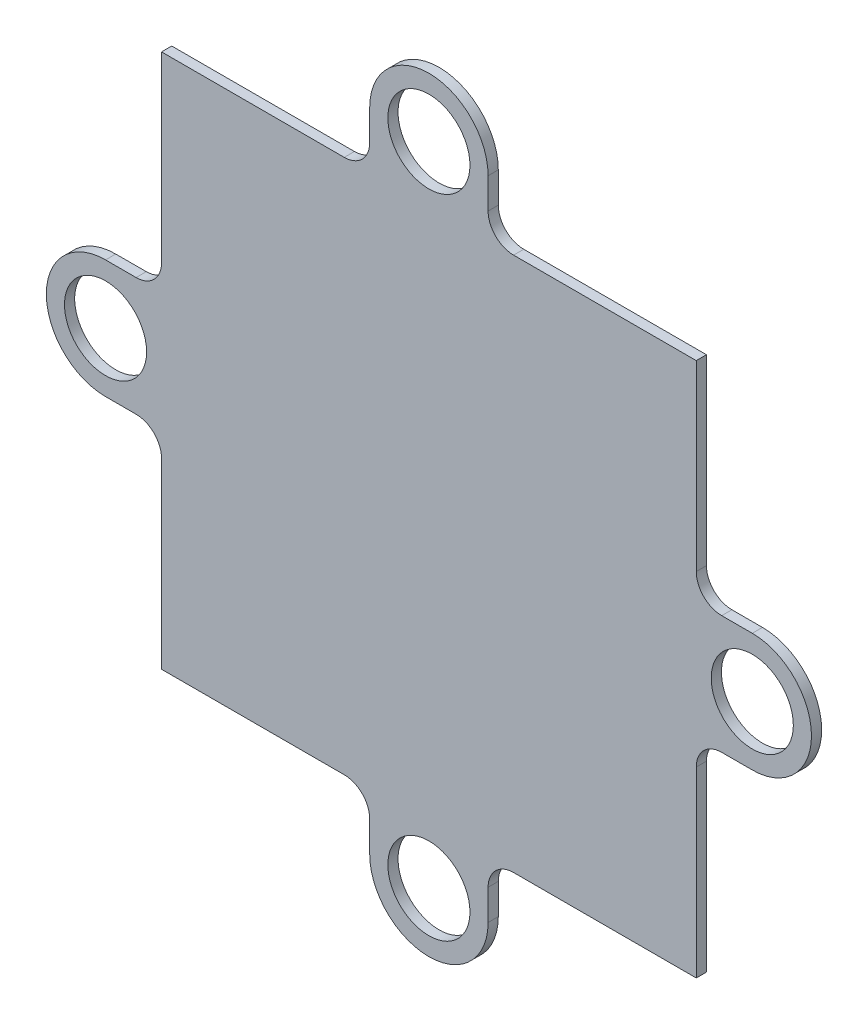
SolidWorks part; units mm, degrees
ref_plane "Front Plane" through (0, 0, 0) normal (0, 0, 1) x (1, 0, 0)
ref_plane "Top Plane" through (0, 0, 0) normal (0, 1, 0) x (1, 0, 0)
ref_plane "Right Plane" through (0, 0, 0) normal (1, 0, 0) x (0, 0, -1)
sketch "Sketch1" plane through (0, 0, 0) normal (0, 0, 1) x (1, 0, 0)
  line L0 (-4.65, 25.4) -> (-4.65, 23)
  line L1 (-21, -21) -> (-6.65, -21)
  line L2 (-21, -21) -> (-21, -6.65)
  line L3 (-21, 21) -> (-6.65, 21)
  line L4 (21, -21) -> (21, -6.65)
  line L5 (-21, -21) -> (21, 21) construction
  line L6 (-21, 21) -> (21, -21) construction
  line L7 (-6.65, 21) -> (-8.7591, 21)
  line L8 (4.65, 25.4) -> (4.65, 23)
  line L9 (6.65, 21) -> (7.1335, 21)
  line L10 (25.4, 4.65) -> (23, 4.65)
  line L11 (21, 6.65) -> (21, 8.7591)
  line L12 (25.4, -4.65) -> (23, -4.65)
  line L13 (21, -6.65) -> (21, -7.1335)
  line L14 (4.65, -25.4) -> (4.65, -23)
  line L15 (6.65, -21) -> (8.7591, -21)
  line L16 (-4.65, -25.4) -> (-4.65, -23)
  line L17 (-6.65, -21) -> (-7.1335, -21)
  line L18 (-25.4, -4.65) -> (-23, -4.65)
  line L19 (-21, -6.65) -> (-21, -8.7591)
  line L20 (-25.4, 4.65) -> (-23, 4.65)
  line L21 (-21, 6.65) -> (-21, 7.1335)
  line L22 (-21, 6.65) -> (-21, 21)
  line L23 (6.65, 21) -> (21, 21)
  line L24 (21, 6.65) -> (21, 21)
  line L25 (6.65, -21) -> (21, -21)
  circle A0 centre (0, 25.4) radius 3.225
  arc A1 (4.65, 25.4) -> (-4.65, 25.4) centre (0, 25.4) ccw
  arc A2 (4.65, 23) -> (6.65, 21) centre (6.65, 23) ccw
  arc A3 (-4.65, 23) -> (-6.65, 21) centre (-6.65, 23) cw
  circle A4 centre (25.4, 0) radius 3.225
  arc A5 (25.4, -4.65) -> (25.4, 4.65) centre (25.4, 0) ccw
  arc A6 (23, -4.65) -> (21, -6.65) centre (23, -6.65) ccw
  arc A7 (23, 4.65) -> (21, 6.65) centre (23, 6.65) cw
  circle A8 centre (0, -25.4) radius 3.225
  arc A9 (-4.65, -25.4) -> (4.65, -25.4) centre (0, -25.4) ccw
  arc A10 (-4.65, -23) -> (-6.65, -21) centre (-6.65, -23) ccw
  arc A11 (4.65, -23) -> (6.65, -21) centre (6.65, -23) cw
  circle A12 centre (-25.4, 0) radius 3.225
  arc A13 (-25.4, 4.65) -> (-25.4, -4.65) centre (-25.4, 0) ccw
  arc A14 (-23, 4.65) -> (-21, 6.65) centre (-23, 6.65) ccw
  arc A15 (-23, -4.65) -> (-21, -6.65) centre (-23, -6.65) cw
  point P0 (0, 0)
  point P53 (0, 0)
  dimension "D1" = 2
extrude "Boss-Extrude1" add sketch "Sketch1" along normal blind 0.8 contours L18 A15 L2 L1 A10 L16 A9 L14 A11 L15 L25 L4 A6 L12 A5 L10 A7 L11 L24 L23 L9 A2 L8 A1 L0 A3 L3 L22 L21 A14 L20 A13 A0 A4 A8 A12
